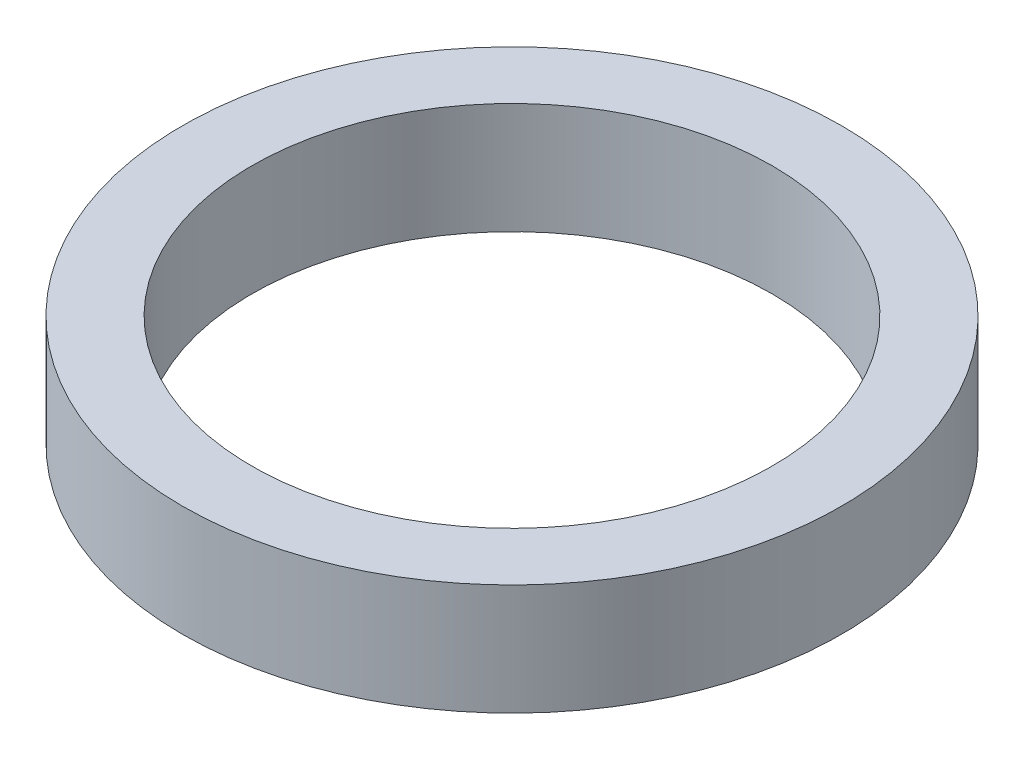
SolidWorks part; units mm, degrees
ref_plane "Front Plane" through (0, 0, 0) normal (0, 0, 1) x (1, 0, 0)
ref_plane "Top Plane" through (0, 0, 0) normal (0, 1, 0) x (1, 0, 0)
ref_plane "Right Plane" through (0, 0, 0) normal (1, 0, 0) x (0, 0, -1)
sketch "Sketch1" plane through (0, 0, 0) normal (0, 1, 0) x (1, 0, 0)
  circle A0 centre (0, 0) radius 30.1625
  dimension "D1" = 60.325
extrude "Boss-Extrude1" add sketch "Sketch1" along normal blind 10.16
sketch "Sketch2" plane through (0, 0, 0) normal (0, -1, 0) x (-1, 0, 0)
  circle A0 centre (0, 0) radius 23.8125
  circle A1 centre (0, 0) radius 30.1625 construction
  dimension "D1" = 6.35
extrude "Cut-Extrude1" cut sketch "Sketch2" against normal through all
